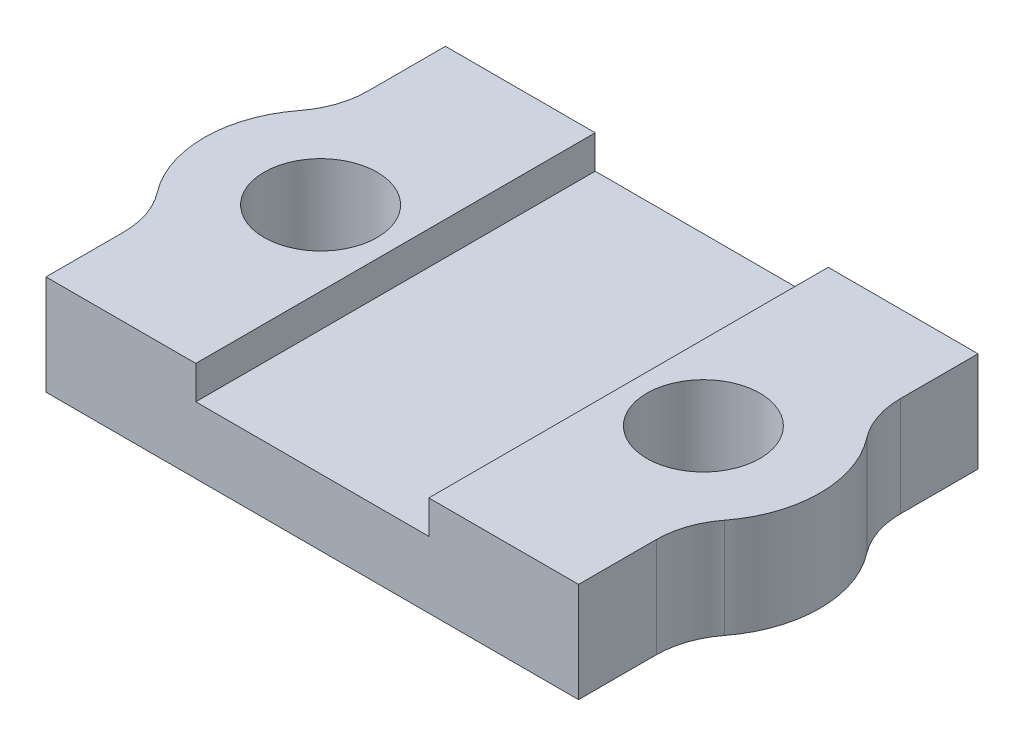
SolidWorks part; units mm, degrees
ref_plane "Alzado" through (0, 0, 0) normal (0, 0, 1) x (1, 0, 0)
ref_plane "Planta" through (0, 0, 0) normal (0, 1, 0) x (1, 0, 0)
ref_plane "Vista lateral" through (0, 0, 0) normal (1, 0, 0) x (0, 0, -1)
sketch "Croquis1" plane through (0, 0, 0) normal (0, 1, 0) x (1, 0, 0)
  line L0 (0, -16.4018) -> (0, 78.9163) construction
  line L1 (-63.9099, 0) -> (63.9099, 0) construction
  line L2 (-8, 6) -> (8, 6)
  line L3 (8, 6) -> (8, 3.6657)
  line L4 (-8, -6) -> (8, -6)
  line L5 (8, -6) -> (8, -3.6657)
  line L6 (-8, -6) -> (-8, -3.6657)
  line L7 (-8, 6) -> (-8, 3.6657)
  circle A0 centre (5.75, 0) radius 1.7
  arc A1 (8.5208, -2.1383) -> (8.5208, 2.1383) centre (5.75, 0) ccw
  arc A2 (8, 3.6657) -> (8.5208, 2.1383) centre (10.5, 3.6657) ccw
  arc A3 (8, -3.6657) -> (8.5208, -2.1383) centre (10.5, -3.6657) cw
  arc A4 (-8, -3.6657) -> (-8.5208, -2.1383) centre (-10.5, -3.6657) ccw
  arc A5 (-8, 3.6657) -> (-8.5208, 2.1383) centre (-10.5, 3.6657) cw
  arc A6 (-8.5208, -2.1383) -> (-8.5208, 2.1383) centre (-5.75, 0) cw
  circle A7 centre (-5.75, 0) radius 1.7
  point P10 (8, 0)
  point P19 (0, 0)
  point P28 (0, -6)
  point P29 (-8, 0)
  point P30 (0, 6)
  dimension "D1" = 3.4
  dimension "D5" = 7
  dimension "D6" = 5
  dimension "D2" = 5.75
  dimension "D3" = 8
  dimension "D4" = 6
extrude "Saliente-Extruir1" add sketch "Croquis1" along normal blind 2
sketch "Croquis5" plane through (0, 2, 0) normal (0, 1, 0) x (1, 0, 0)
  line L0 (3.5, -6) -> (3.5, 6)
  line L1 (-8, -6) -> (8, -6) construction
  line L2 (8, 6) -> (-8, 6) construction
  line L7 (3.5, 6) -> (8, 6)
  line L8 (8, -6) -> (8, -3.6657)
  line L9 (-8, -6) -> (8, -6)
  line L10 (8, -6) -> (8, -3.6657)
  line L11 (-8, -6) -> (8, -6) construction
  line L12 (8, 3.6657) -> (8, 6)
  line L13 (8, 3.6657) -> (8, 6)
  line L14 (3.5, -6) -> (8, -6)
  circle A11 centre (5.75, 0) radius 1.7
  arc A12 (8, 3.6657) -> (8.5208, 2.1383) centre (10.5, 3.6657) ccw
  arc A13 (8.5208, -2.1383) -> (8.5208, 2.1383) centre (5.75, 0) ccw
  arc A14 (8.5208, -2.1383) -> (8, -3.6657) centre (10.5, -3.6657) ccw
  arc A15 (8, 3.6657) -> (8.5208, 2.1383) centre (10.5, 3.6657) ccw
  arc A16 (8.5208, -2.1383) -> (8.5208, 2.1383) centre (5.75, 0) ccw
  arc A17 (8.5208, -2.1383) -> (8, -3.6657) centre (10.5, -3.6657) ccw
  circle A18 centre (5.75, 0) radius 1.7
  point P6 (0, -6)
  dimension "D1" = 3.5
  dimension "D2" = 0
  dimension "D3" = 0
  dimension "D4" = 0
extrude "Saliente-Extruir3" add sketch "Croquis5" along normal blind 1
mirror "Simetría1" about plane through (0, 0, 0) normal (1, 0, 0) of "Saliente-Extruir3"
